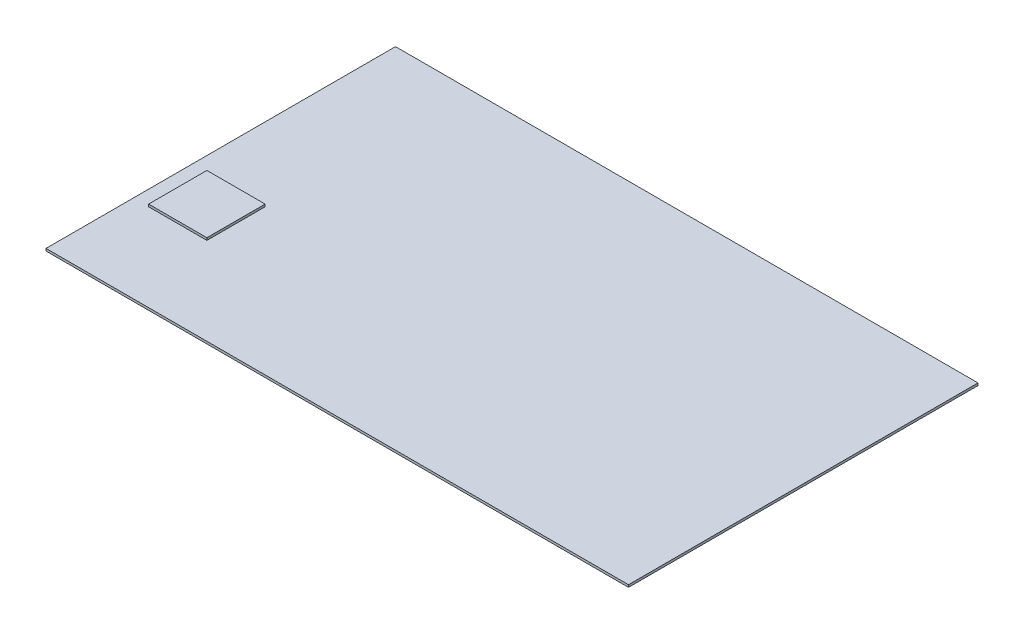
SolidWorks part; units mm, degrees
ref_plane "Front Plane" through (0, 0, 0) normal (0, 0, 1) x (1, 0, 0)
ref_plane "Top Plane" through (0, 0, 0) normal (0, 1, 0) x (1, 0, 0)
ref_plane "Right Plane" through (0, 0, 0) normal (1, 0, 0) x (0, 0, -1)
sketch "Sketch1" plane through (0, 0, 0) normal (0, 1, 0) x (1, 0, 0)
  line L1 (-37.5457, 57.4524) -> (212.4543, 57.4524)
  line L2 (-37.5457, 57.4524) -> (-37.5457, -92.5476)
  line L3 (-37.5457, -92.5476) -> (212.4543, -92.5476)
  line L4 (212.4543, 57.4524) -> (212.4543, -92.5476)
  dimension "D1" = 250
  dimension "D2" = 150
extrude "Boss-Extrude1" add sketch "Sketch1" along normal blind 1
sketch "Sketch2" plane through (0, 1, 0) normal (0, 1, 0) x (1, 0, 0)
  line L0 (-18.4957, -30.0476) -> (-18.4957, -55.0476) construction
  line L1 (-5.9957, -30.0476) -> (-30.9957, -30.0476)
  line L2 (-5.9957, -30.0476) -> (-5.9957, -55.0476)
  line L3 (-5.9957, -55.0476) -> (-30.9957, -55.0476)
  line L4 (-30.9957, -30.0476) -> (-30.9957, -55.0476)
  line L5 (-37.5457, -92.5476) -> (212.4543, -92.5476) construction
  line L6 (-5.9957, -42.5476) -> (-30.9957, -42.5476) construction
  line L7 (-37.5457, 57.4524) -> (-37.5457, -92.5476) construction
  dimension "D1" = 25
  dimension "D2" = 25
  dimension "D3" = 50
  dimension "D4" = 19.05
extrude "Boss-Extrude2" add sketch "Sketch2" along normal blind 1
